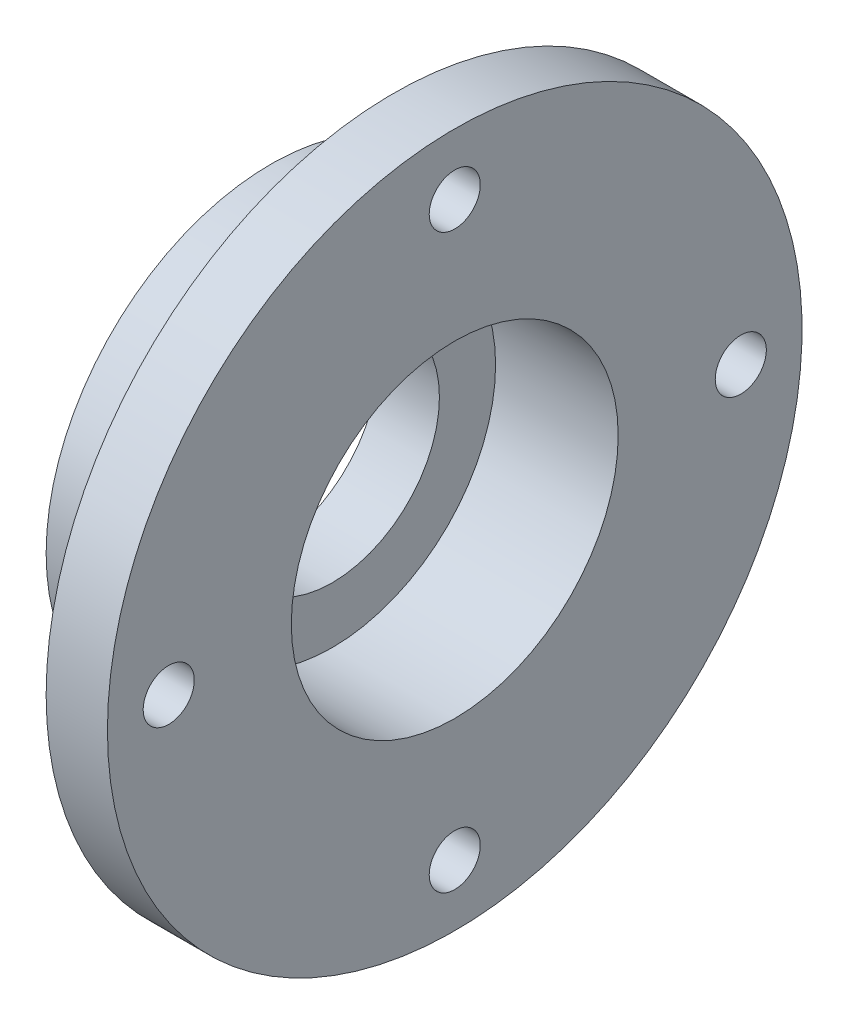
SolidWorks part; units mm, degrees
ref_plane "Front Plane" through (0, 0, 0) normal (0, 0, 1) x (1, 0, 0)
ref_plane "Top Plane" through (0, 0, 0) normal (0, 1, 0) x (1, 0, 0)
ref_plane "Right Plane" through (0, 0, 0) normal (1, 0, 0) x (0, 0, -1)
sketch "Sketch1" plane through (0, 0, 0) normal (0, 0, 1) x (1, 0, 0)
  line L0 (-41.9627, 0) -> (0, 0) construction
  line L1 (0, 0) -> (0, 73.744) construction
  line L2 (0, 34) -> (-6, 34)
  line L3 (-6, 34) -> (-6, 22)
  line L4 (-6, 22) -> (-18, 22)
  line L5 (-18, 22) -> (-18, 0)
  line L6 (0, 34) -> (0, 16)
  line L7 (0, 16) -> (-12, 16)
  line L8 (-12, 16) -> (-12, 0)
  line L9 (-18, 0) -> (-12, 0)
  line L10 (-12, 0) -> (-12.3538, -0.5415)
  line L11 (-18, 10.5) -> (-12, 10.5)
  dimension "D1" = 16
  dimension "D2" = 12
  dimension "D3" = 6
  dimension "D4" = 6
  dimension "D5" = 6
  dimension "D6" = 12
  dimension "D7" = 10.5
revolve "Revolve1" add sketch "Sketch1" angle 360 about L0
sketch "Sketch2" plane through (-6, 0, 0) normal (-1, 0, 0) x (0, 0, 1)
  line L0 (0, 34) -> (0, 22) construction
  circle A0 centre (0, 28) radius 2.5
  circle A1 centre (28, 0) radius 2.5
  circle A2 centre (0, -28) radius 2.5
  circle A3 centre (-28, 0) radius 2.5
  circle A4 centre (0, 0) radius 34 construction
  circle A5 centre (0, 0) radius 22 construction
  point P12 (0, 0)
  point P17 (0, 28)
  dimension "D1" = 5
  dimension "D3" = 4
extrude "Cut-Extrude1" cut sketch "Sketch2" against normal through all
